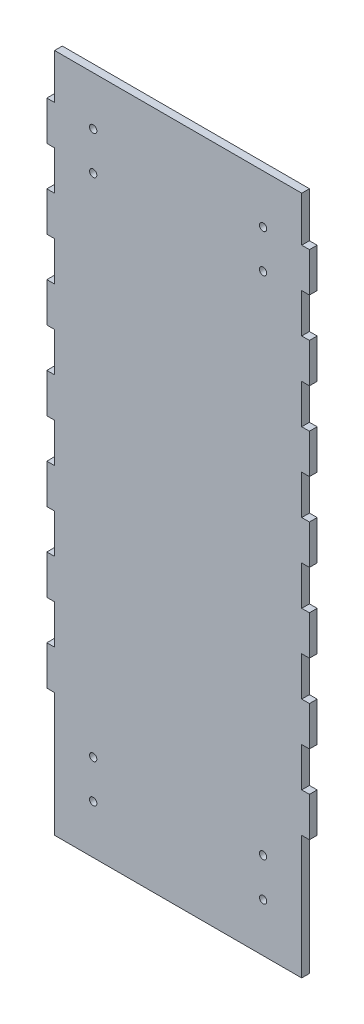
SolidWorks part; units mm, degrees
material "Acrylic (Medium-high impact)"
ref_plane "Front Plane" through (0, 0, 0) normal (0, 0, 1) x (1, 0, 0)
ref_plane "Top Plane" through (0, 0, 0) normal (0, 1, 0) x (1, 0, 0)
ref_plane "Right Plane" through (0, 0, 0) normal (1, 0, 0) x (0, 0, -1)
sketch "Sketch1" plane through (0, 0, 0) normal (0, 0, 1) x (1, 0, 0)
  line L5 (0, 279.4) -> (101.6, 279.4)
  line L87 (101.6, 0) -> (0, 0)
  line L88 (50.8, 279.4) -> (50.8, 0) construction
  line L90 (0, 0) -> (-3.175, 0)
  line L110 (-3.175, 66.9636) -> (-3.175, 50.8)
  line L187 (-3.175, 99.2836) -> (-3.175, 83.12)
  line L199 (-3.175, 66.9636) -> (0, 66.9636)
  line L200 (-3.175, 50.8) -> (0, 50.8)
  line L221 (0, 50.8) -> (0, 34.64)
  line L222 (0, 34.64) -> (0, 0)
  line L223 (-3.175, 99.2836) -> (0, 99.2836)
  line L224 (-3.175, 83.12) -> (0, 83.12)
  line L225 (0, 83.12) -> (0, 66.96)
  line L226 (-3.175, 131.6036) -> (-3.175, 115.44)
  line L227 (-3.175, 131.6036) -> (0, 131.6036)
  line L228 (-3.175, 115.44) -> (0, 115.44)
  line L241 (0, 115.44) -> (0, 99.28)
  line L242 (-3.175, 163.9236) -> (-3.175, 147.76)
  line L243 (-3.175, 163.9236) -> (0, 163.9236)
  line L244 (-3.175, 147.76) -> (0, 147.76)
  line L245 (0, 147.76) -> (0, 131.6)
  line L246 (-3.175, 196.2436) -> (-3.175, 180.08)
  line L247 (-3.175, 196.2436) -> (0, 196.2436)
  line L248 (-3.175, 180.08) -> (0, 180.08)
  line L249 (0, 180.08) -> (0, 163.92)
  line L250 (-3.175, 228.5636) -> (-3.175, 212.4)
  line L251 (-3.175, 228.5636) -> (0, 228.5636)
  line L252 (-3.175, 212.4) -> (0, 212.4)
  line L253 (0, 212.4) -> (0, 196.24)
  line L254 (-3.175, 260.8836) -> (-3.175, 244.72)
  line L255 (-3.175, 260.8836) -> (0, 260.8836)
  line L256 (-3.175, 244.72) -> (0, 244.72)
  line L257 (0, 244.72) -> (0, 228.56)
  line L258 (0, 279.4) -> (0, 260.8836)
  line L259 (101.6, 279.4) -> (101.6, 260.8836)
  line L260 (101.6, 244.72) -> (101.6, 228.56)
  line L261 (104.775, 244.72) -> (101.6, 244.72)
  line L262 (104.775, 260.8836) -> (101.6, 260.8836)
  line L263 (104.775, 260.8836) -> (104.775, 244.72)
  line L264 (101.6, 212.4) -> (101.6, 196.24)
  line L265 (104.775, 212.4) -> (101.6, 212.4)
  line L266 (104.775, 228.5636) -> (101.6, 228.5636)
  line L267 (104.775, 228.5636) -> (104.775, 212.4)
  line L268 (101.6, 180.08) -> (101.6, 163.92)
  line L269 (104.775, 180.08) -> (101.6, 180.08)
  line L270 (104.775, 196.2436) -> (101.6, 196.2436)
  line L271 (104.775, 196.2436) -> (104.775, 180.08)
  line L272 (101.6, 147.76) -> (101.6, 131.6)
  line L273 (104.775, 147.76) -> (101.6, 147.76)
  line L274 (104.775, 163.9236) -> (101.6, 163.9236)
  line L275 (104.775, 163.9236) -> (104.775, 147.76)
  line L276 (101.6, 115.44) -> (101.6, 99.28)
  line L277 (104.775, 115.44) -> (101.6, 115.44)
  line L278 (104.775, 131.6036) -> (101.6, 131.6036)
  line L279 (104.775, 131.6036) -> (104.775, 115.44)
  line L280 (101.6, 83.12) -> (101.6, 66.96)
  line L281 (104.775, 83.12) -> (101.6, 83.12)
  line L282 (104.775, 99.2836) -> (101.6, 99.2836)
  line L283 (101.6, 34.64) -> (101.6, 0)
  line L284 (101.6, 50.8) -> (101.6, 34.64)
  line L285 (104.775, 50.8) -> (101.6, 50.8)
  line L286 (104.775, 66.9636) -> (101.6, 66.9636)
  line L287 (104.775, 99.2836) -> (104.775, 83.12)
  line L288 (104.775, 66.9636) -> (104.775, 50.8)
  line L289 (101.6, 0) -> (104.775, 0)
  dimension "D1" = 279.4
  dimension "D3" = 50.8
  dimension "D4" = 3.175
  dimension "D2" = 101.6
extrude "Boss-Extrude1" add sketch "Sketch1" along normal blind 3.175
sketch "Sketch2" plane through (0, 0, 3.175) normal (0, 0, 1) x (1, 0, 0)
  line L2 (50.8, 279.4) -> (50.8, 0) construction
  line L4 (50.8, 139.7) -> (-3.175, 139.7) construction
  line L6 (-3.175, 50.8) -> (-3.175, 0) construction
  line L7 (101.6, 0) -> (0, 0) construction
  circle A0 centre (15.875, 20) radius 1.5
  circle A1 centre (15.875, 35.75) radius 1.5
  circle A2 centre (15.875, 243.65) radius 1.5
  circle A3 centre (15.875, 259.4) radius 1.5
  circle A4 centre (85.725, 259.4) radius 1.5
  circle A5 centre (85.725, 243.65) radius 1.5
  circle A6 centre (85.725, 35.75) radius 1.5
  circle A7 centre (85.725, 20) radius 1.5
  dimension "D1" = 3
  dimension "D2" = 3
  dimension "D3" = 15.75
  dimension "D4" = 19.05
  dimension "D5" = 20
extrude "Cut-Extrude1" cut sketch "Sketch2" against normal up to surface (3.175 mm away) up to face at (50.8, 154.7657, 0)
sketch "Sketch3" [suppressed] plane through (0, 0, 3.175) normal (0, 0, 1) x (1, 0, 0)
  line L0 (20.375, 5) -> (20.375, 93.1333)
  line L1 (20.375, 93.1333) -> (81.225, 93.1333)
  line L2 (81.225, 93.1333) -> (81.225, 5)
  line L3 (81.225, 5) -> (20.375, 5)
  line L4 (101.6, 0) -> (0, 0) construction
  line L5 (50.8, 279.4) -> (50.8, 0) construction
  circle A0 centre (15.875, 20) radius 1.5 construction
  circle A1 centre (85.725, 20) radius 1.5 construction
  dimension "D1" = 5
  dimension "D2" = 4.5
  dimension "D3" = 4.5
  dimension "D4" = 279.4
  dimension "D5" = 93.1333
extrude "Cut-Extrude2" [suppressed] cut sketch "Sketch3" against normal up to surface (3.175 mm away)
equation "\"D8@Sketch1\"=\"D6@Sketch1\""
equation "\"D5@Sketch3\"=\"D4@Sketch3\"/3"
